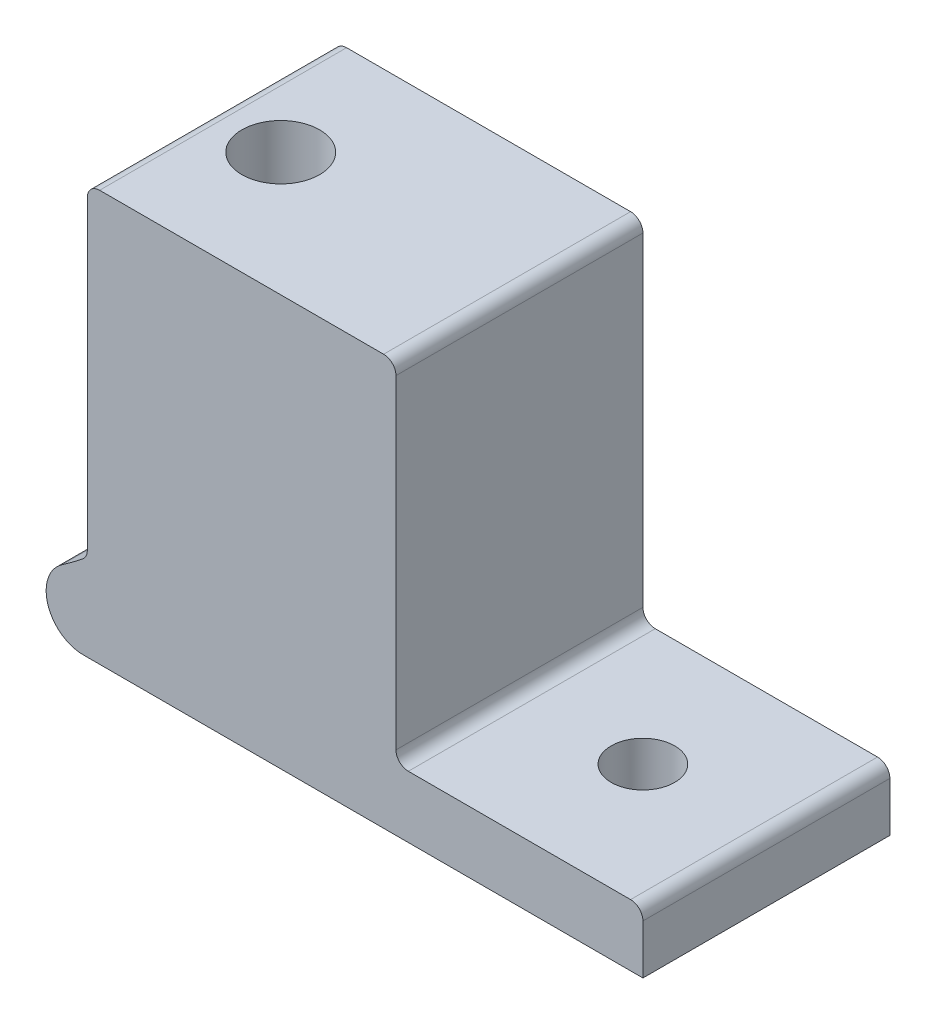
SolidWorks part; units mm, degrees
ref_plane "Front Plane" through (0, 0, 0) normal (0, 0, 1) x (1, 0, 0)
ref_plane "Top Plane" through (0, 0, 0) normal (0, 1, 0) x (1, 0, 0)
ref_plane "Right Plane" through (0, 0, 0) normal (1, 0, 0) x (0, 0, -1)
sketch "Sketch1" plane through (0, 0, 0) normal (0, 0, 1) x (1, 0, 0)
  line L0 (0, -39) -> (81.9545, -39) construction
  line L1 (81.9545, -39) -> (81.9545, -32.65)
  line L2 (81.9545, -32.65) -> (56.5545, -32.65)
  line L3 (56.5545, -32.65) -> (56.5545, 3.23)
  line L4 (56.5545, 3.23) -> (24.8045, 3.23)
  line L5 (24.8045, 3.23) -> (24.8045, -3.12)
  line L6 (24.8045, -3.12) -> (38.875, -3.12)
  line L7 (24.3795, -39) -> (81.9545, -39)
  line L8 (69.2545, -32.65) -> (69.2545, -39) construction
  arc A0 (-38.875, -3.12) -> (38.875, -3.12) centre (0, 0) ccw construction
  arc A1 (38.875, -3.12) -> (22.2098, -32.0582) centre (0, 0) cw
  arc A2 (22.2098, -32.0582) -> (24.3795, -39) centre (24.3795, -35.19) ccw
  dimension "D1" = 25.4
  dimension "D7" = 39
  dimension "D8" = 3.81
  dimension "D2" = 35.88
  dimension "D3" = 31.75
  dimension "D4" = 6.35
  dimension "D5" = 14.0705
  dimension "D6" = 81.9545
  dimension "D9" = 6.35
extrude "Boss-Extrude1" add sketch "Sketch1" along normal mid plane 25.4
sketch "Sketch2" plane through (0, 0, 0) normal (0, 1, 0) x (1, 0, 0)
  line L0 (81.9545, 12.7) -> (56.5545, -12.7) construction
  line L1 (81.9545, -12.7) -> (56.5545, -12.7) construction
  line L2 (56.5545, -12.7) -> (56.5545, 12.7) construction
  circle A0 centre (69.2545, 0) radius 3.2639
  dimension "D1" = 6.5278
extrude "Cut-Extrude1" cut sketch "Sketch2" against normal through all both and the other way through all
sketch "Sketch3" plane through (0, 3.23, 0) normal (0, 1, 0) x (1, 0, 0)
  line L0 (32, 12.7) -> (32, -12.7) construction
  line L1 (56.5545, 12.7) -> (24.8045, 12.7) construction
  line L2 (56.5545, -12.7) -> (24.8045, -12.7) construction
  circle A0 centre (32, 0) radius 4
  circle A1 centre (32, 0) radius 4 construction
extrude "Cut-Extrude2" cut sketch "Sketch3" against normal blind 31.75
sketch "Sketch4" plane through (24.8045, 0, 0) normal (-1, 0, 0) x (0, 0, 1)
  line L0 (12.7, -39) -> (-12.7, -39) construction
  line L1 (-12.7, 3.23) -> (-9.5885, 3.23)
  line L2 (-12.7, 3.23) -> (-12.7, -39)
  line L3 (-12.7, -39) -> (-9.5885, -39)
  line L4 (-9.5885, 3.23) -> (-9.5885, -39)
  line L6 (12.7, 3.23) -> (9.5885, 3.23)
  line L7 (12.7, 3.23) -> (12.7, -39)
  line L8 (12.7, -39) -> (9.5885, -39)
  line L9 (9.5885, 3.23) -> (9.5885, -39)
  dimension "D1" = 19.177
extrude "Boss-Extrude2" add sketch "Sketch4" against normal up to surface (31.75 mm away) up to face at (56.5545, -14.71, 0)
fillet "Fillet4" radius 1.27 6 edges at (81.9545, -32.65, 0) (56.5545, -32.65, 0) (56.5545, 3.23, 0) (24.8045, 3.23, 0) (24.8045, -30.0954, -11.1443) (24.8045, -30.0954, 11.1442)
